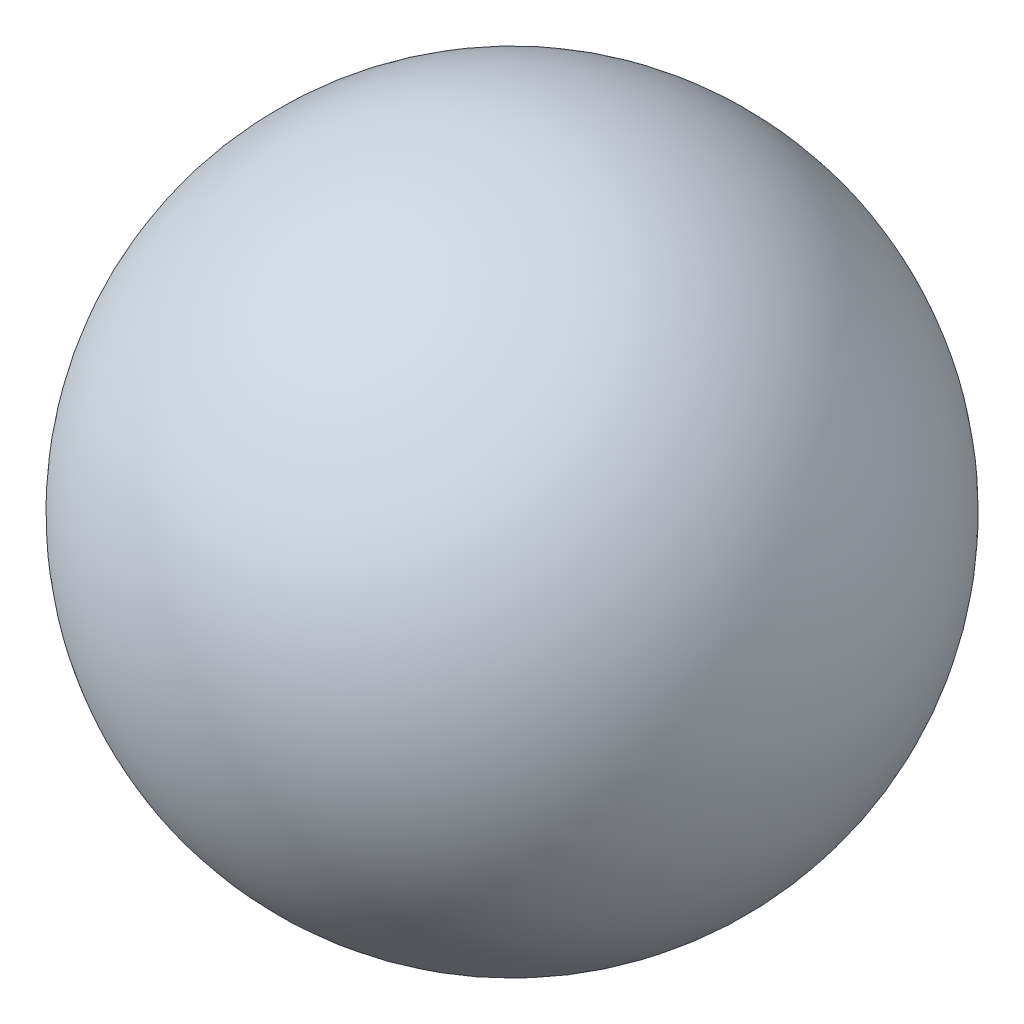
SolidWorks part; units mm, degrees
material "AISI 304"
ref_plane "前视基准面" through (0, 0, 0) normal (0, 0, 1) x (1, 0, 0)
ref_plane "上视基准面" through (0, 0, 0) normal (0, 1, 0) x (1, 0, 0)
ref_plane "右视基准面" through (0, 0, 0) normal (1, 0, 0) x (0, 0, -1)
sketch "Sketch1" plane through (0, 0, 0) normal (0, 1, 0) x (1, 0, 0)
  line L0 (0, -4) -> (0, 4) construction
  line L1 (0, 4) -> (0, -4)
  arc A0 (0, -4) -> (0, 4) centre (0, 0) ccw
  point P5 (0, 0)
  dimension "D1" = 8
revolve "Revolve1" add sketch "Sketch1" angle 360 about L0
